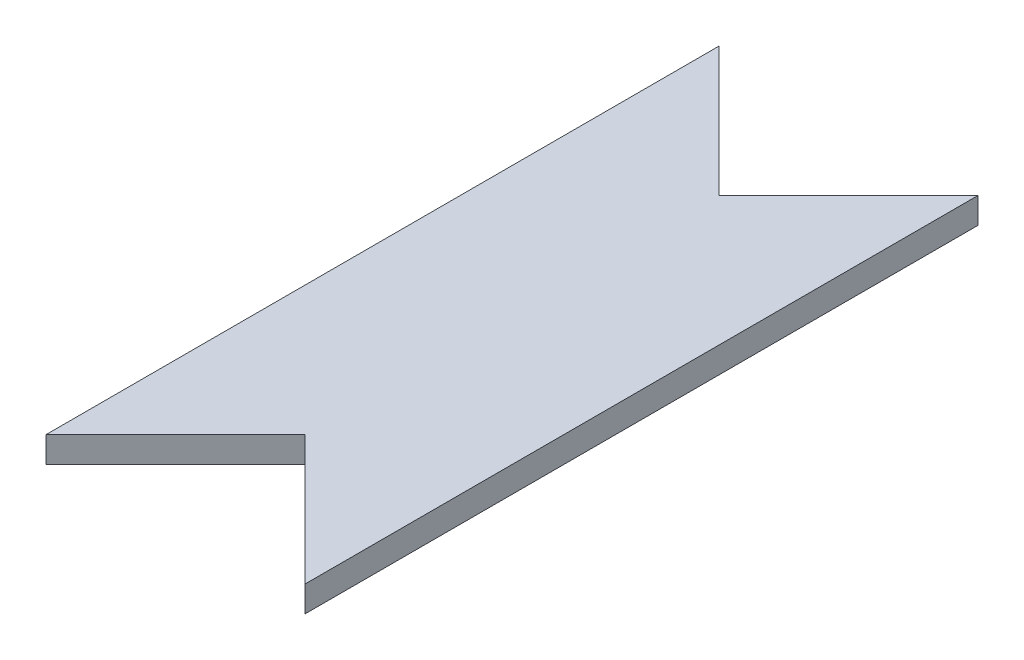
SolidWorks part; units mm, degrees
ref_plane "Front Plane" through (0, 0, 0) normal (0, 0, 1) x (1, 0, 0)
ref_plane "Top Plane" through (0, 0, 0) normal (0, 1, 0) x (1, 0, 0)
ref_plane "Right Plane" through (0, 0, 0) normal (1, 0, 0) x (0, 0, -1)
sketch "Sketch1" plane through (0, 0, 0) normal (0, 1, 0) x (1, 0, 0)
  line L0 (3.8142, -10.7992) -> (-2.5358, -17.1492)
  line L1 (-2.5358, -17.1492) -> (-2.5358, 15.8708)
  line L2 (-2.5358, 15.8708) -> (3.8142, 9.5208)
  line L4 (10.1642, 15.8708) -> (3.8142, 9.5208)
  line L5 (10.1642, -17.1492) -> (10.1642, 15.8708)
  line L6 (3.8142, -10.7992) -> (10.1642, -17.1492)
extrude "Boss-Extrude1" add sketch "Sketch1" along normal blind 1.27
